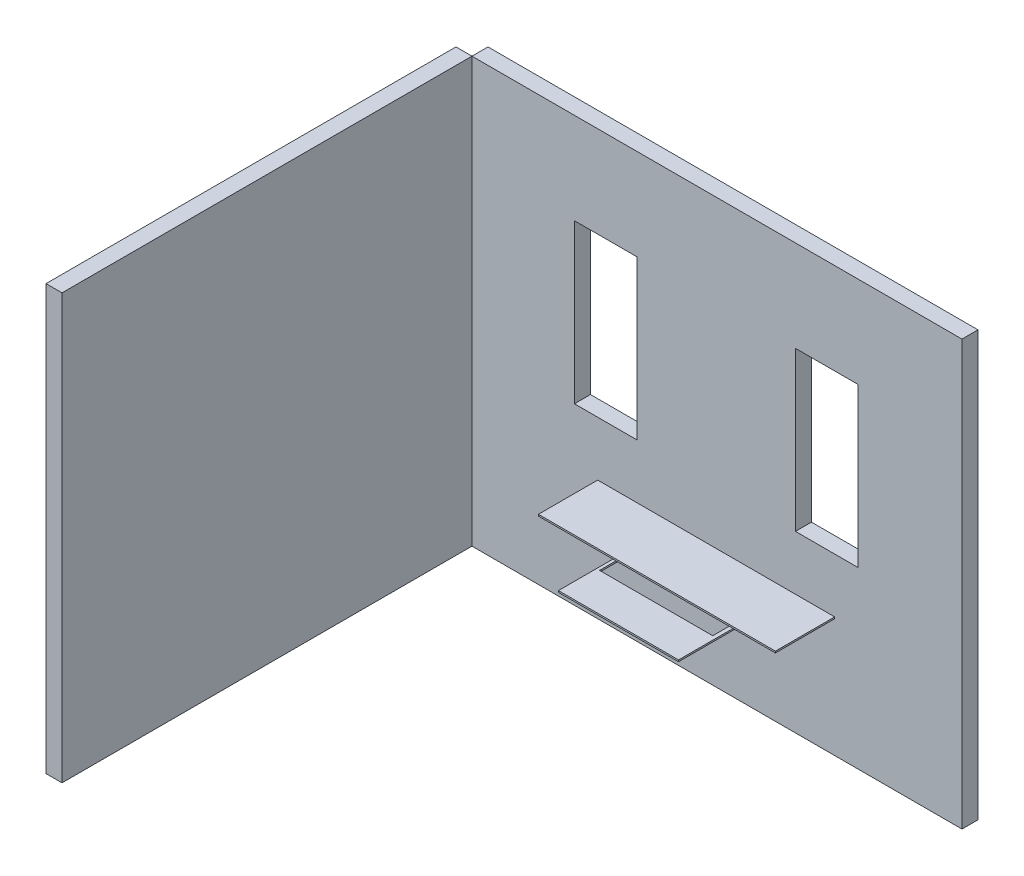
SolidWorks part; units mm, degrees
ref_plane "Plano frontal" through (0, 0, 0) normal (0, 0, 1) x (1, 0, 0)
ref_plane "Plano superior" through (0, 0, 0) normal (0, 1, 0) x (1, 0, 0)
ref_plane "Plano direito" through (0, 0, 0) normal (1, 0, 0) x (0, 0, -1)
sketch "Esboço6" plane through (0, 0, 0) normal (0, 0, 1) x (1, 0, 0)
  line L1 (0, 0) -> (3060, 0)
  line L2 (0, 0) -> (0, 2650)
  line L3 (0, 2650) -> (3060, 2650)
  line L4 (3060, 0) -> (3060, 2650)
extrude "Ressalto-extrusão2" add sketch "Esboço6" along normal blind 100
sketch "Esboço7" plane through (0, 0, 100) normal (0, 0, 1) x (1, 0, 0)
  line L2 (2020, 2080) -> (2020, 1090)
  line L3 (640, 2080) -> (640, 1090)
  line L4 (640, 2080) -> (1030, 2080)
  line L5 (1030, 2080) -> (1030, 1090)
  line L6 (1030, 1090) -> (640, 1090)
  line L7 (2020, 1090) -> (2410, 1090)
  line L8 (2410, 1090) -> (2410, 2080)
  line L9 (2410, 2080) -> (2020, 2080)
extrude "Corte-extrusão1" cut sketch "Esboço7" against normal blind 749
sketch "Esboço8" plane through (0, 0, 100) normal (0, 0, 1) x (1, 0, 0)
  line L1 (0, 2650) -> (-100, 2650)
  line L2 (0, 2650) -> (0, 0)
  line L3 (0, 0) -> (-100, 0)
  line L4 (-100, 2650) -> (-100, 0)
extrude "Ressalto-extrusão3" add sketch "Esboço8" along normal blind 2560 separate body
sketch "Esboço14" plane through (0, 0, 100) normal (0, 0, 1) x (1, 0, 0)
  line L0 (785, 740) -> (2265, 740)
  line L2 (0, 0) -> (3060, 0) construction
  line L3 (20, 740) -> (20, 750)
  line L4 (2265, 740) -> (2265, 750)
  line L6 (20, 0) -> (2020, 0)
  line L7 (2265, 750) -> (785, 750)
  line L8 (785, 750) -> (785, 740)
extrude "Ressalto-extrusão6" add sketch "Esboço14" along normal blind 370 contours L0 L4 L7 L8
sketch "Esboço16" plane through (0, 0, 0) normal (0, 0, 1) x (1, 0, 0)
  line L0 (1150, 640) -> (1900, 640)
  line L3 (1900, 640) -> (1900, 630)
  line L4 (1900, 630) -> (1150, 630)
  line L5 (1150, 630) -> (1150, 640)
extrude "Ressalto-extrusão7" add sketch "Esboço16" along normal blind 710
sketch "Esboço17" plane through (0, 630, 0) normal (0, -1, 0) x (1, 0, 0)
  line L0 (1169.068, 100) -> (1876.1537, 100)
  line L1 (1150, 100) -> (1900, 100) construction
  line L2 (1876.1537, 100) -> (1876.1537, 472.6246)
  line L4 (1169.068, 100) -> (1169.068, 472.6246)
  line L5 (1169.068, 472.6246) -> (1876.1537, 472.6246)
extrude "Corte-extrusão3" cut sketch "Esboço17" against normal blind 70
ref_plane "Plano1" through (3060, 2650, 100) normal (0, 1, 0) x (1, 0, 0)
